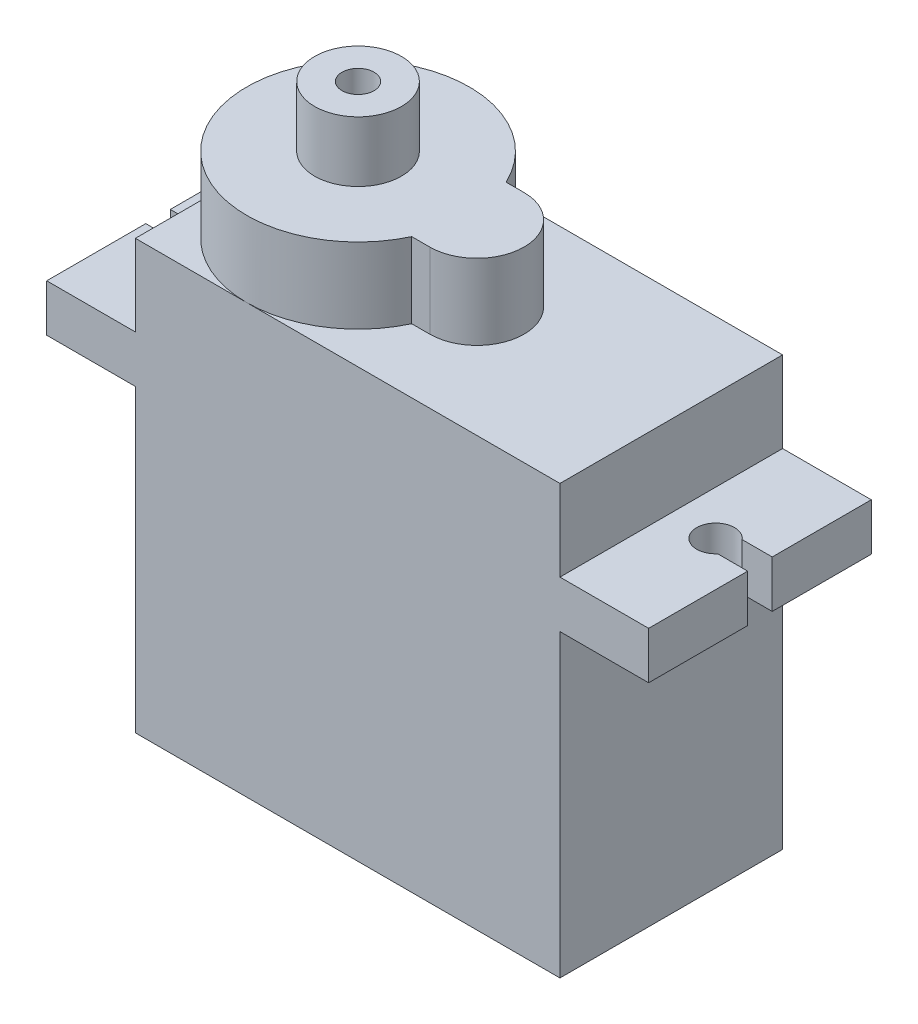
SolidWorks part; units mm, degrees
ref_plane "Front Plane" through (0, 0, 0) normal (0, 0, 1) x (1, 0, 0)
ref_plane "Top Plane" through (0, 0, 0) normal (0, 1, 0) x (1, 0, 0)
ref_plane "Right Plane" through (0, 0, 0) normal (1, 0, 0) x (0, 0, -1)
sketch "Sketch1" plane through (0, 0, 0) normal (0, 1, 0) x (1, 0, 0)
  line L1 (0, 0) -> (22.5, 0)
  line L2 (0, 0) -> (0, 11.8)
  line L3 (0, 11.8) -> (22.5, 11.8)
  line L4 (22.5, 0) -> (22.5, 11.8)
  dimension "D1" = 22.5
  dimension "D2" = 11.8
extrude "Boss-Extrude1" add sketch "Sketch1" along normal blind 22.7
ref_plane "Plane1" through (0, 15.9, 0) normal (0, -1, 0) x (-1, 0, 0)
sketch "Sketch2" plane through (0, 15.9, 0) normal (0, -1, 0) x (-1, 0, 0)
  line L0 (-22.5, 11.8) -> (-27.2, 11.8)
  line L1 (-27.2, 11.8) -> (-27.2, 0)
  line L2 (-27.2, 0) -> (-22.5, 0)
  line L3 (0, 11.8) -> (4.7, 11.8)
  line L4 (0, 0) -> (0, 11.8)
  line L5 (0, 11.8) -> (-22.5, 11.8)
  line L6 (-22.5, 11.8) -> (-22.5, 0)
  line L7 (-22.5, 0) -> (0, 0)
  line L8 (0, 0) -> (0, 11.8)
  line L10 (-22.5, 11.8) -> (-22.5, 0)
  line L12 (4.7, 11.8) -> (4.7, 0)
  line L13 (4.7, 0) -> (0, 0)
  dimension "D2" = 4.7
  dimension "D1" = 0
extrude "Boss-Extrude2" add sketch "Sketch2" against normal blind 2.5
sketch "Sketch3" plane through (0, 22.7, 0) normal (0, 1, 0) x (1, 0, 0)
  line L0 (22.5, 11.8) -> (0, 11.8) construction
  line L1 (0, 11.8) -> (0, 0) construction
  line L2 (0, 0) -> (22.5, 0) construction
  line L3 (5.9, 5.9) -> (12.2, 5.9) construction
  line L4 (12.2, 8.4) -> (11.2442, 8.4)
  line L5 (12.2, 3.4) -> (11.2442, 3.4)
  arc A0 (11.2442, 8.4) -> (11.2442, 3.4) centre (5.9, 5.9) ccw
  arc A1 (12.2, 3.4) -> (12.2, 8.4) centre (12.2, 5.9) ccw
  point P11 (14.7, 5.9)
  dimension "D1" = 2.5
  dimension "D2" = 8.8
extrude "Boss-Extrude3" add sketch "Sketch3" along normal blind 4
sketch "Sketch4" plane through (0, 18.4, 0) normal (0, 1, 0) x (1, 0, 0)
  line L0 (27.2, 0) -> (22.5, 0) construction
  line L1 (22.5, 11.8) -> (27.2, 11.8) construction
  line L2 (0, 0) -> (-4.7, 0) construction
  line L3 (-4.7, 11.8) -> (0, 11.8) construction
  line L4 (27.2, 0) -> (22.5, 0) construction
  line L5 (22.5, 11.8) -> (27.2, 11.8) construction
  line L6 (0, 0) -> (-4.7, 0) construction
  line L7 (-4.7, 11.8) -> (0, 11.8) construction
  line L8 (-2.35, 11.8) -> (-2.35, 0) construction
  line L9 (24.85, 11.8) -> (24.85, 0) construction
  line L10 (-2.35, 5.9) -> (-4.7, 5.9) construction
  line L11 (-4.7, 0) -> (-4.7, 11.8) construction
  line L12 (24.85, 5.9) -> (27.2, 5.9) construction
  line L13 (27.2, 11.8) -> (27.2, 0) construction
  line L14 (-4.7, 6.55) -> (-4.7, 5.25)
  line L15 (27.2, 6.55) -> (27.2, 5.25)
  line L16 (-4.7, 6.55) -> (-3.1099, 6.55)
  line L17 (-4.7, 5.25) -> (-3.1099, 5.25)
  line L18 (27.2, 6.55) -> (25.6099, 6.55)
  line L19 (27.2, 5.25) -> (25.6099, 5.25)
  arc A0 (-3.1099, 5.25) -> (-3.1099, 6.55) centre (-2.35, 5.9) ccw
  arc A1 (25.6099, 6.55) -> (25.6099, 5.25) centre (24.85, 5.9) ccw
  point P26 (-4.7, 5.9)
  point P29 (27.2, 5.9)
  dimension "D1" = 2
  dimension "D2" = 1.3
extrude "Cut-Extrude1" cut sketch "Sketch4" against normal up to surface (2.5 mm away) up to face at (24.85, 15.9, -5.9)
sketch "Sketch5" plane through (0, 26.7, 0) normal (0, 1, 0) x (1, 0, 0)
  circle A0 centre (5.9, 5.9) radius 2.3
  circle A1 centre (5.9, 5.9) radius 0.85
  dimension "D1" = 4.6
  dimension "D2" = 1.7
extrude "Boss-Extrude4" add sketch "Sketch5" along normal blind 3.2
